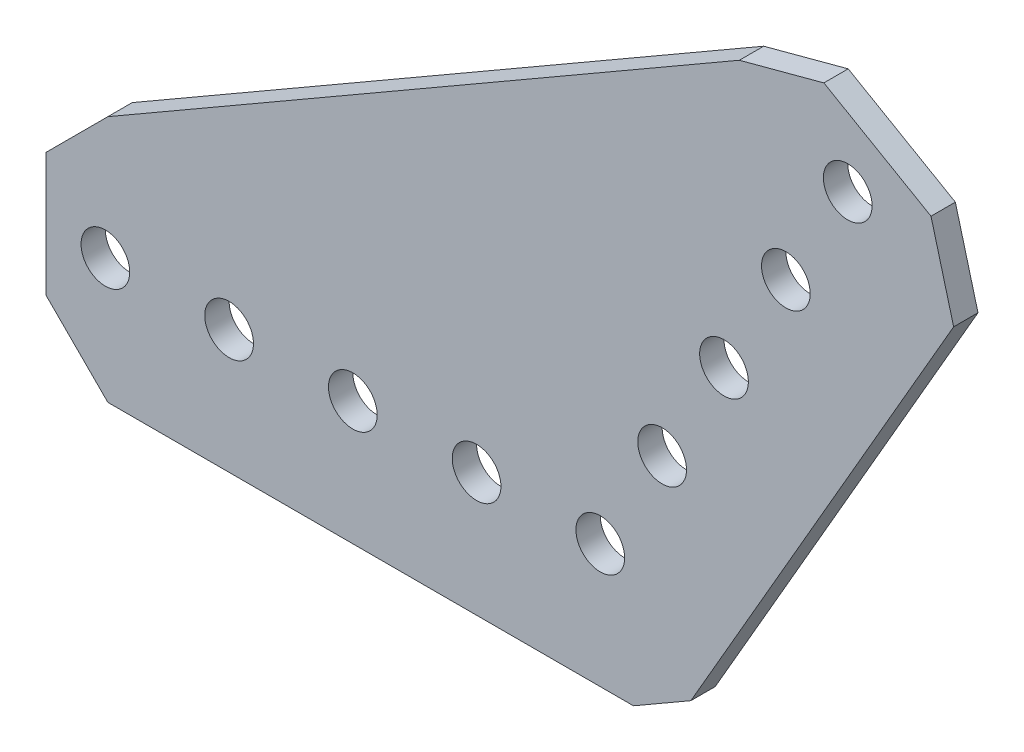
SolidWorks part; units mm, degrees
material "5052-H32"
ref_plane "Front Plane" through (0, 0, 0) normal (0, 0, 1) x (1, 0, 0)
ref_plane "Top Plane" through (0, 0, 0) normal (0, 1, 0) x (1, 0, 0)
ref_plane "Right Plane" through (0, 0, 0) normal (1, 0, 0) x (0, 0, -1)
ref_plane "Plane1" through (0, 0, -1.25) normal (0, 0, -1) x (-1, 0, 0)
sketch "Sketch1" plane through (0, 0, -1.25) normal (0, 0, -1) x (-1, 0, 0)
  line L0 (-3.403, -12.7) -> (50.546, -12.7)
  line L1 (50.546, -12.7) -> (56.896, -6.35)
  line L2 (56.896, -6.35) -> (56.896, 6.35)
  line L3 (56.896, 6.35) -> (50.546, 12.7)
  line L4 (50.546, 12.7) -> (-14.2745, 50.1241)
  line L5 (-14.2745, 50.1241) -> (-22.9487, 52.4484)
  line L6 (-22.9487, 52.4484) -> (-33.9473, 46.0984)
  line L7 (-33.9473, 46.0984) -> (-36.2715, 37.4241)
  line L8 (-36.2715, 37.4241) -> (-9.297, -9.297)
  line L9 (-9.297, -9.297) -> (-3.403, -12.7)
  circle A0 centre (12.7, 0) radius 2.5
  circle A1 centre (25.4, 0) radius 2.5
  circle A2 centre (0, 0) radius 2.5
  circle A3 centre (50.8, 0) radius 2.5
  circle A4 centre (38.1, 0) radius 2.5
  circle A5 centre (-25.4, 43.9941) radius 2.5
  circle A6 centre (-19.05, 32.9956) radius 2.5
  circle A7 centre (-12.7, 21.997) radius 2.5
  circle A8 centre (-6.35, 10.9985) radius 2.5
extrude "Boss-Extrude1" add sketch "Sketch1" against normal blind 2.5
